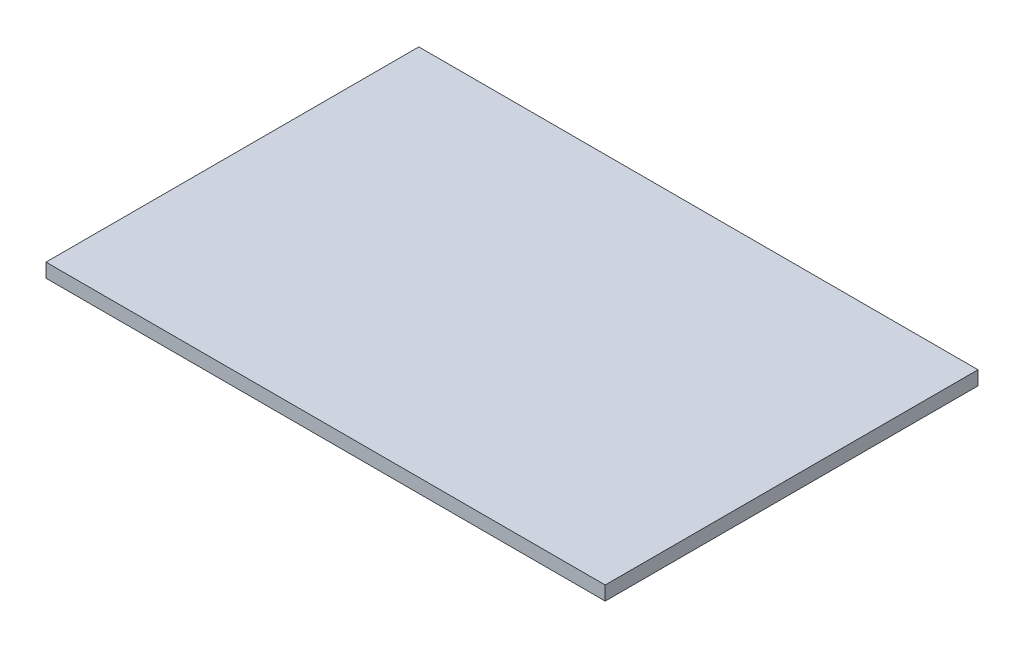
SolidWorks part; units mm, degrees
ref_plane "Alzado" through (0, 0, 0) normal (0, 0, 1) x (1, 0, 0)
ref_plane "Planta" through (0, 0, 0) normal (0, 1, 0) x (1, 0, 0)
ref_plane "Vista lateral" through (0, 0, 0) normal (1, 0, 0) x (0, 0, -1)
sketch "Croquis1" plane through (0, 0, 0) normal (0, 1, 0) x (1, 0, 0)
  line L1 (-6, 4) -> (6, 4)
  line L2 (-6, 4) -> (-6, -4)
  line L3 (-6, -4) -> (6, -4)
  line L4 (6, 4) -> (6, -4)
  line L5 (-6, 4) -> (6, -4) construction
  line L6 (-6, -4) -> (6, 4) construction
  point P0 (0, 0)
  point P6 (0, 0)
  point P8 (0, 0)
  dimension "D1" = 6
  dimension "D2" = 8
extrude "Saliente-Extruir1" add sketch "Croquis1" along normal blind 0.3
